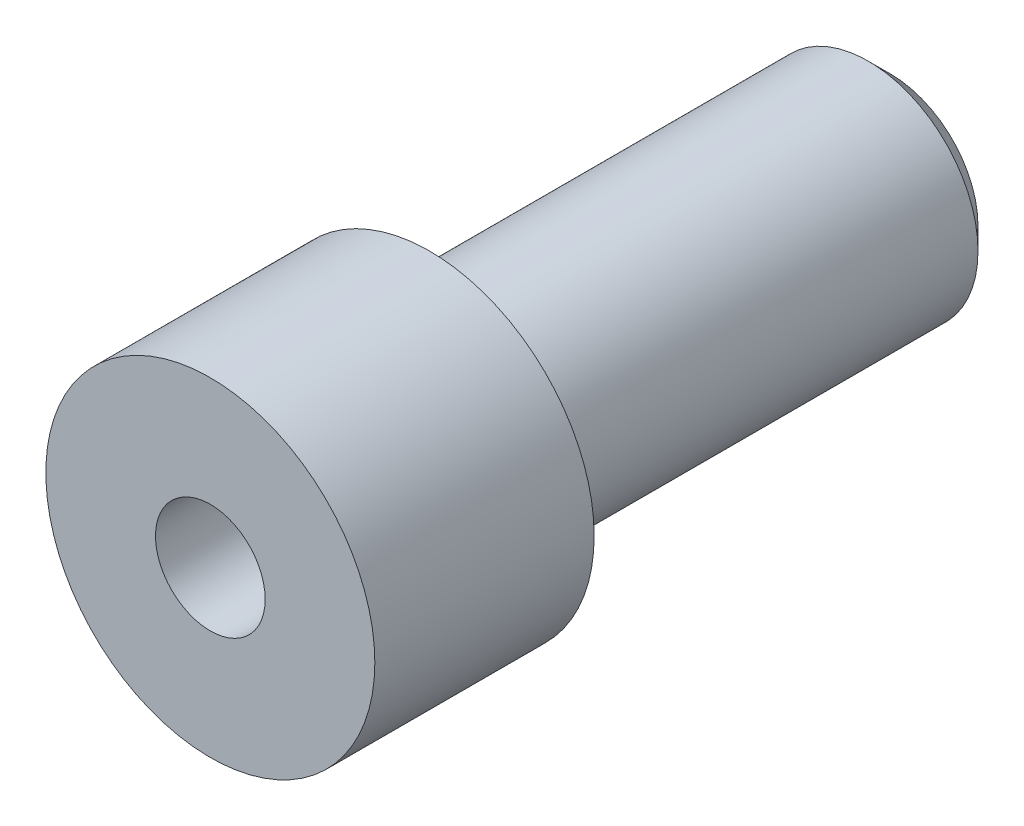
SolidWorks part; units mm, degrees
material "黄铜"
ref_plane "前视基准面" through (0, 0, 0) normal (0, 0, 1) x (1, 0, 0)
ref_plane "上视基准面" through (0, 0, 0) normal (0, 1, 0) x (1, 0, 0)
ref_plane "右视基准面" through (0, 0, 0) normal (1, 0, 0) x (0, 0, -1)
other "Configuration Table"
sketch "草图1" plane through (0, 0, 0) normal (0, 0, 1) x (1, 0, 0)
  circle A0 centre (0, 0) radius 1.5
  dimension "D1" = 3
extrude "凸台-拉伸1" add sketch "草图1" along normal blind 2
sketch "草图2" plane through (0, 0, 0) normal (0, 0, -1) x (-1, 0, 0)
  circle A0 centre (0, 0) radius 1
  dimension "D1" = 2
extrude "凸台-拉伸2" add sketch "草图2" along normal blind 4.2
chamfer "倒角1" distance 0.2 angle 45 1 edges at (-1, 0, -4.2)
hole_wizard "大小mm 暗销孔1" positions "草图3" profile "草图4" hole size "Ø1.0" standard "GB"
sketch "草图3" plane through (0, 0, 2) normal (0, 0, 1) x (1, 0, 0)
  point P0 (0, 0)
sketch "草图4" plane through (0, 0, 2) normal (1, 0, 0) x (0, -1, 0)
  line L0 (0, 0) -> (0, 5.5004)
  line L1 (0, 5.5004) -> (0.5, 5.2)
  line L2 (0.5, 5.2) -> (0.5, 0)
  line L5 (0.5, 0) -> (0, 0)
  line L10 (0, 5.5004) -> (-0.5, 5.2) construction
  line L11 (0, -6.35) -> (0, 107.95) construction
  dimension "孔直径" = 1
  dimension "孔深度" = 5.2
  dimension "导头角度" = 118
